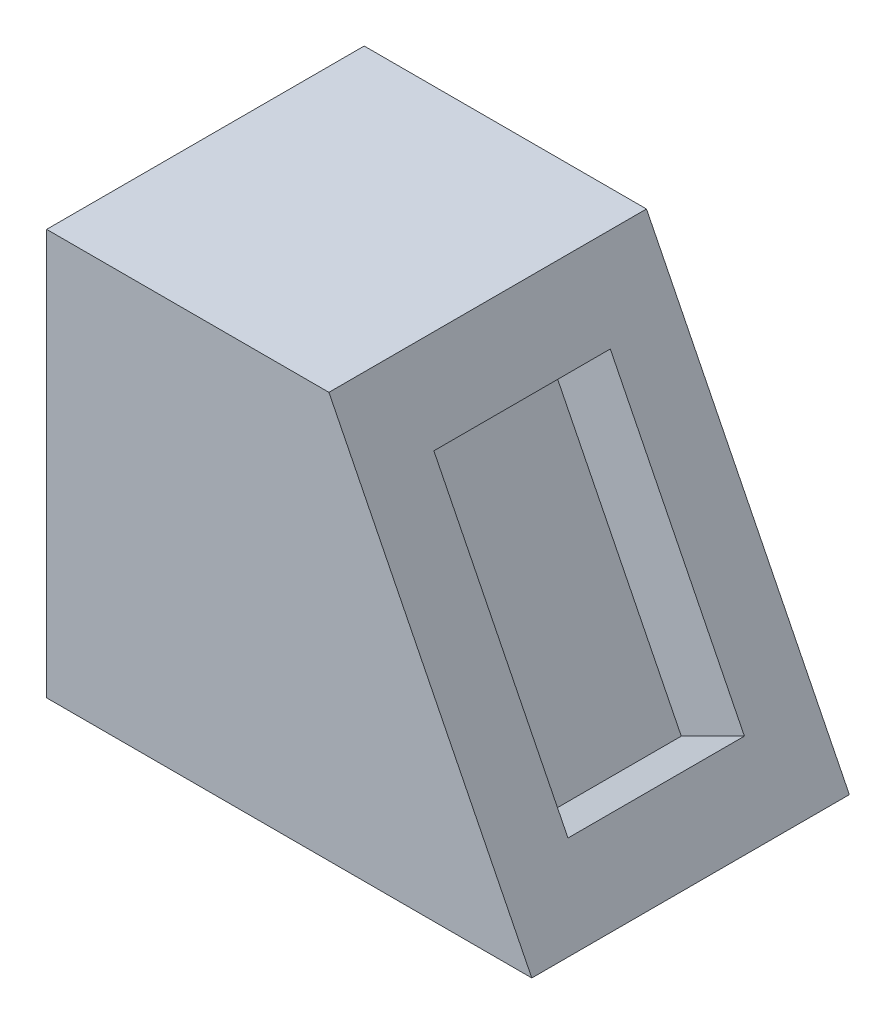
SolidWorks part; units mm, degrees
ref_plane "Front Plane" through (0, 0, 0) normal (0, 0, 1) x (1, 0, 0)
ref_plane "Top Plane" through (0, 0, 0) normal (0, 1, 0) x (1, 0, 0)
ref_plane "Right Plane" through (0, 0, 0) normal (1, 0, 0) x (0, 0, -1)
sketch "Sketch1" plane through (0, 0, 0) normal (0, 0, 1) x (1, 0, 0)
  line L0 (0, 0) -> (275, 0)
  line L1 (0, 0) -> (0, 230)
  line L2 (0, 230) -> (160, 230)
  line L3 (160, 230) -> (275, 0)
  dimension "D1" = 275
  dimension "D2" = 230
  dimension "D3" = 160
extrude "Boss-Extrude1" add sketch "Sketch1" against normal blind 180
ref_plane "Plane1" through (228.9443, 114.4721, 0) normal (0.8944, 0.4472, 0) x (0, 0, -1)
sketch "Sketch3" plane through (228.9443, 114.4721, 0) normal (0.8944, 0.4472, 0) x (0, 0, -1)
  line L0 (40, -79.4098) -> (40, 90.5902)
  line L1 (40, 90.5902) -> (140, 90.5902)
  line L2 (140, 90.5902) -> (140, -79.4098)
  line L3 (140, -79.4098) -> (40, -79.4098)
  line L4 (0, -122.9837) -> (0, 134.1641) construction
  line L5 (180, -122.9837) -> (0, -122.9837) construction
  point P4 (0, 5.5902)
  point P7 (40, 5.5902)
  point P10 (90, -122.9837)
  point P11 (90, -79.4098)
  dimension "D1" = 170
  dimension "D2" = 100
extrude "Cut-Extrude4" cut sketch "Sketch3" against normal blind 50
